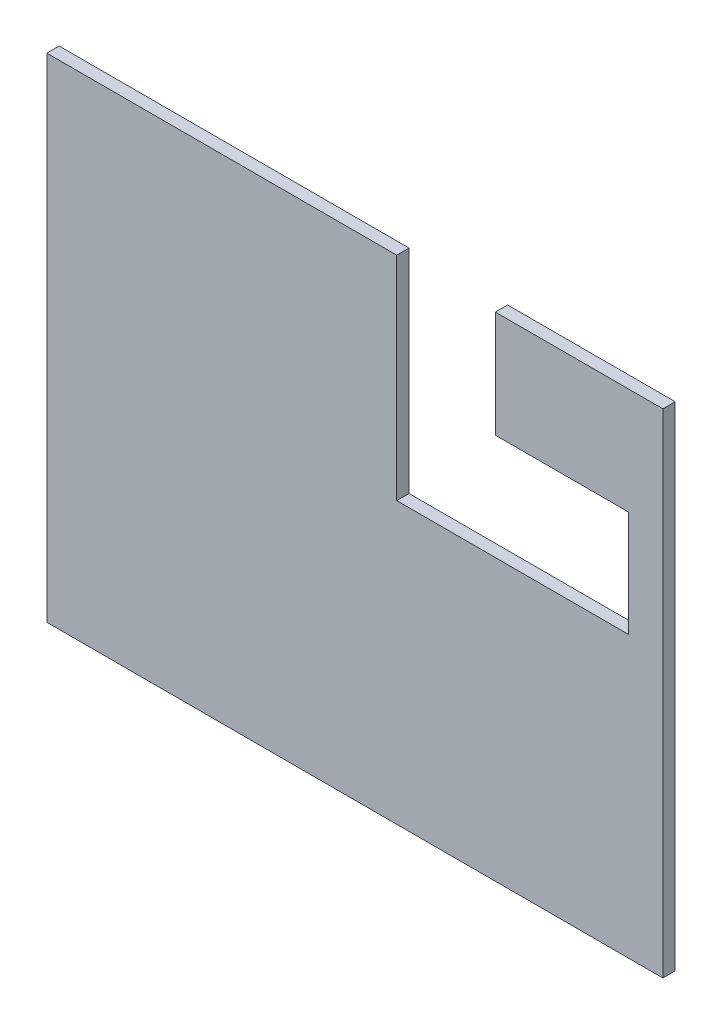
SolidWorks part; units mm, degrees
ref_plane "Alzado" through (0, 0, 0) normal (0, 0, 1) x (1, 0, 0)
ref_plane "Planta" through (0, 0, 0) normal (0, 1, 0) x (1, 0, 0)
ref_plane "Vista lateral" through (0, 0, 0) normal (1, 0, 0) x (0, 0, -1)
sketch "Croquis1" plane through (0, 0, 0) normal (0, 0, 1) x (1, 0, 0)
  line L1 (0, 0) -> (5000, 0)
  line L2 (0, 0) -> (0, 4000)
  line L3 (0, 4000) -> (5000, 4000)
  line L4 (5000, 0) -> (5000, 4000)
  dimension "D1" = 5000
  dimension "D2" = 4000
extrude "Saliente-Extruir1" add sketch "Croquis1" along normal blind 100
sketch "Croquis2" plane through (0, 0, 100) normal (0, 0, 1) x (1, 0, 0)
  line L0 (4720, 3135) -> (4720, 2275)
  line L1 (5000, 0) -> (5000, 4000) construction
  line L2 (4720, 3135) -> (3640, 3135)
  line L3 (3640, 3135) -> (3640, 4000)
  line L4 (5000, 4000) -> (0, 4000) construction
  line L5 (2840, 4000) -> (2840, 2275)
  line L6 (2840, 2275) -> (4720, 2275)
  line L7 (3640, 4000) -> (2840, 4000)
  point P10 (3640, 3567.5)
  dimension "D1" = 280
  dimension "D2" = 865
  dimension "D3" = 800
  dimension "D4" = 1360
  dimension "D5" = 860
extrude "Cortar-Extruir1" cut sketch "Croquis2" against normal blind 100
